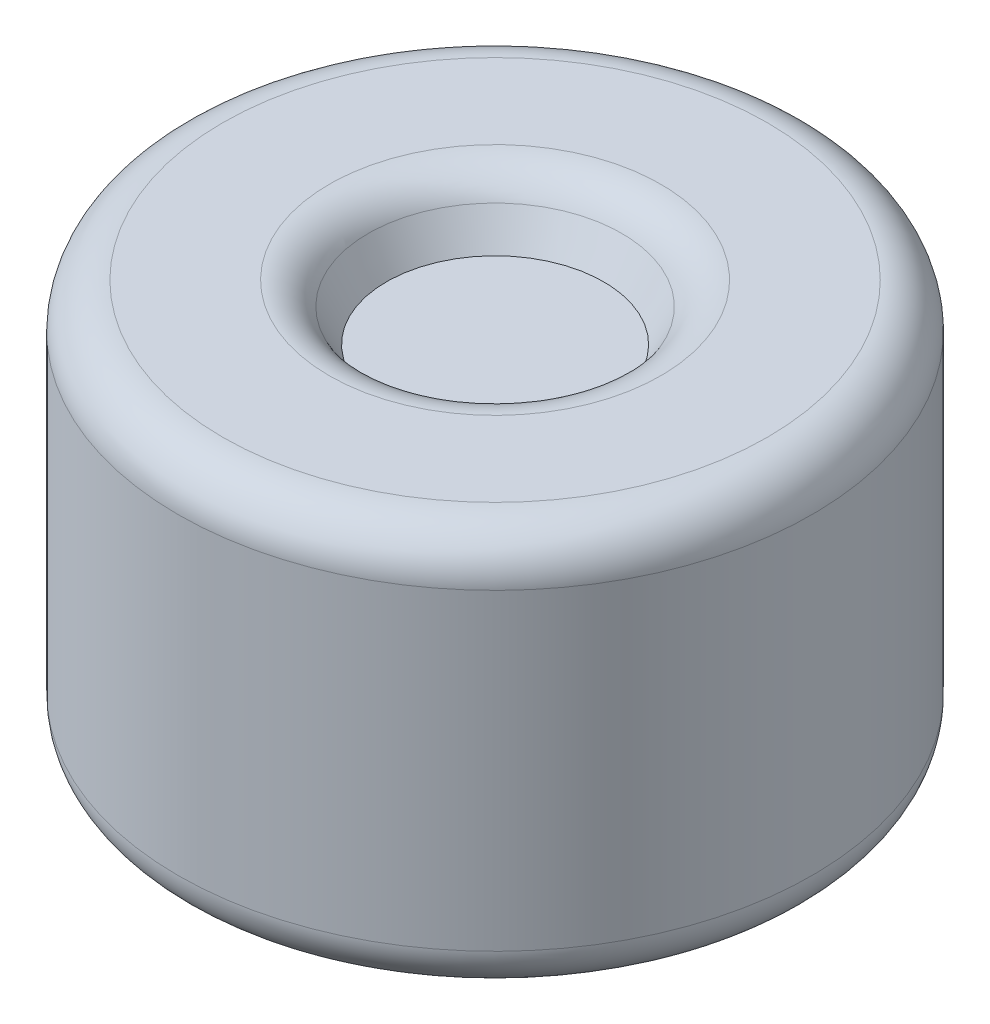
SolidWorks part; units mm, degrees
ref_plane "Alzado" through (0, 0, 0) normal (0, 0, 1) x (1, 0, 0)
ref_plane "Planta" through (0, 0, 0) normal (0, 1, 0) x (1, 0, 0)
ref_plane "Vista lateral" through (0, 0, 0) normal (1, 0, 0) x (0, 0, -1)
sketch "Sketch1" plane through (0, 0, 0) normal (0, 1, 0) x (1, 0, 0)
  circle A0 centre (0, 0) radius 284
  dimension "D1" = 568
extrude "Boss-Extrude1" add sketch "Sketch1" along normal mid plane 360
sketch "Sketch2" plane through (0, 180, 0) normal (0, 1, 0) x (1, 0, 0)
  circle A0 centre (0, 0) radius 125
  dimension "D1" = 250
extrude "Cut-Extrude1" cut sketch "Sketch2" against normal blind 50 draft 29
fillet "Fillet1" radius 40 1 edges at (0, 180, 284)
fillet "Fillet2" radius 40 1 edges at (0, 180, 125)
fillet "Fillet3" radius 40 1 edges at (0, -180, 284)
